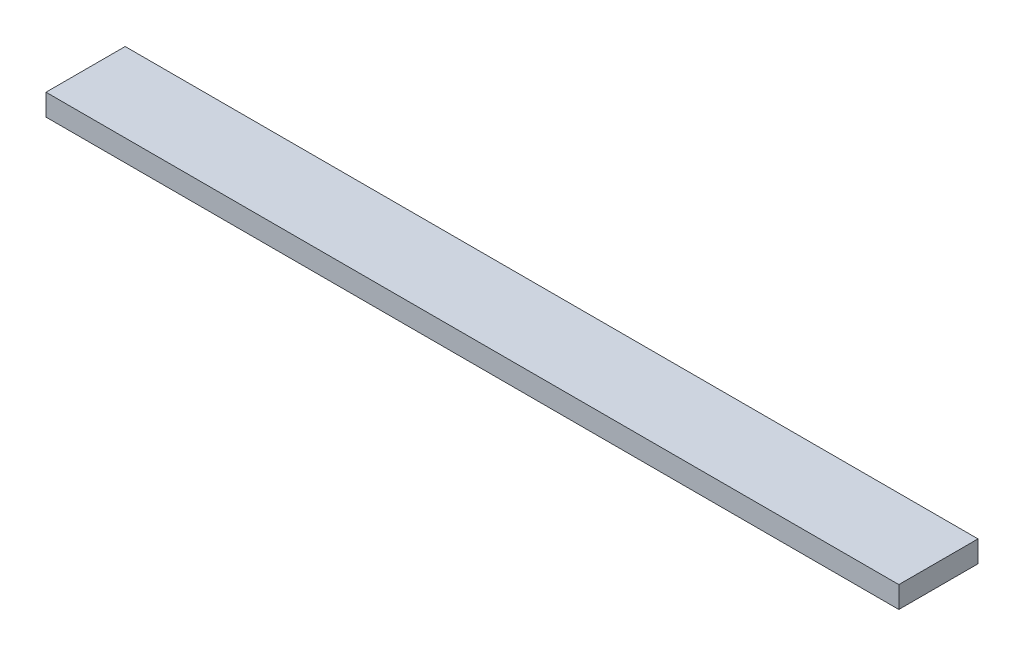
SolidWorks part; units mm, degrees
material "Pine"
ref_plane "Front Plane" through (0, 0, 0) normal (0, 0, 1) x (1, 0, 0)
ref_plane "Top Plane" through (0, 0, 0) normal (0, 1, 0) x (1, 0, 0)
ref_plane "Right Plane" through (0, 0, 0) normal (1, 0, 0) x (0, 0, -1)
sketch "Sketch1" plane through (0, 0, 0) normal (0, 1, 0) x (1, 0, 0)
  line L1 (0, 0) -> (752.475, 0)
  line L2 (0, 0) -> (0, 69.85)
  line L3 (0, 69.85) -> (752.475, 69.85)
  line L4 (752.475, 0) -> (752.475, 69.85)
  dimension "D1" = 69.85
  dimension "D2" = 752.475
extrude "Boss-Extrude1" add sketch "Sketch1" along normal blind 19.05
